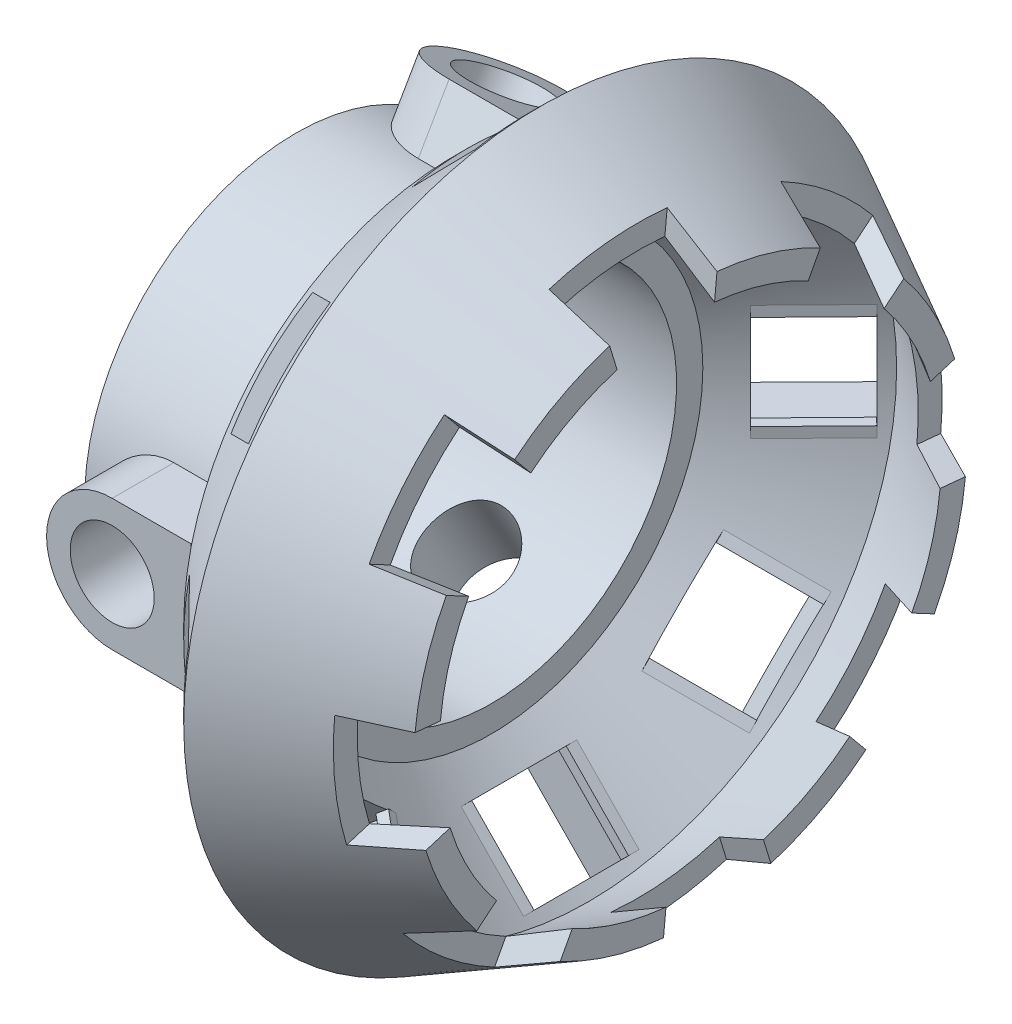
SolidWorks part; units mm, degrees
other "标注1"
sketch "草图8" plane through (-2.7147, -6.8585, 6.8585) normal (-0.2235, -0.0225, 0.9745) x (-0.1799, 0.9835, -0.0185)
ref_plane "前视基准面" through (0, 0, 0) normal (0, 0, 1) x (1, 0, 0)
ref_plane "上视基准面" through (0, 0, 0) normal (0, 1, 0) x (1, 0, 0)
ref_plane "右视基准面" through (0, 0, 0) normal (1, 0, 0) x (0, 0, -1)
sketch "草图1" plane through (0, 0, 0) normal (0, 0, 1) x (1, 0, 0)
  line L0 (0.7876, 3.525) -> (4.3576, 3.525)
  line L4 (4.7876, 4.025) -> (0.7876, 4.025)
  line L5 (0.7876, 4.025) -> (0.7876, 3.525)
  line L7 (7.7746, 6.7877) -> (11.1354, 5)
  line L8 (11.1354, 5) -> (11.1354, 4.5)
  line L9 (11.1354, 4.5) -> (8.6961, 5.8707)
  line L10 (4.3576, 3.525) -> (5.4612, 3.525) construction
  line L11 (7.6354, 5.8) -> (7.6354, 0) construction
  line L12 (0, 0) -> (8.3011, 0) construction
  line L13 (8.1304, 5.305) -> (7.6354, 5.8) construction
  line L14 (6.8503, 4.025) -> (8.6961, 5.8707)
  line L16 (11.1354, 4.5) -> (11.1354, -0.8919) construction
  line L17 (8.1304, 5.305) -> (11.1637, 2.2717) construction
  line L20 (4.7691, 3.525) -> (6.8503, 3.525)
  line L22 (4.3576, 3.525) -> (4.7691, 3.525)
  line L23 (6.1249, 5.138) -> (7.7746, 6.7877)
  line L24 (4.7876, 4.025) -> (7.3502, 4.025) construction
  line L25 (6.1249, 5.138) -> (6.1249, 4.025)
  line L26 (4.7876, 4.025) -> (6.1249, 4.025)
  line L27 (6.8503, 4.025) -> (6.8503, 3.525)
  dimension "D1" = 4.5
  dimension "D2" = 3.525
  dimension "D3" = 0.5
  dimension "D4" = 4
  dimension "D5" = 0.8
  dimension "D6" = 0.7
  dimension "D7" = 5.8
  dimension "D8" = 1.3
  dimension "D9" = 0.5
  dimension "D10" = 3.5
  dimension "D11" = 45
revolve "旋转1" add sketch "草图1" angle 360 about L12
sketch "草图2" plane through (0, 0, 0) normal (0, 1, 0) x (1, 0, 0)
  line L1 (3.0145, -5.257) -> (4.0717, -5.257) construction
  line L8 (6.1249, -5.138) -> (7.7746, -6.7877) construction
  line L9 (5.2766, -6.5082) -> (7.495, -4.2897)
  line L10 (5.2766, -6.5082) -> (6.4787, -7.7103)
  line L11 (6.4787, -7.7103) -> (8.6971, -5.4918)
  line L12 (7.495, -4.2897) -> (8.6971, -5.4918)
  line L13 (5.2766, -6.5082) -> (8.6971, -5.4918) construction
  line L14 (6.4787, -7.7103) -> (7.495, -4.2897) construction
  line L15 (0, 0) -> (-4.3641, 0) construction
  line L16 (6.9869, -6) -> (5.8776, -7.1092) construction
  line L17 (6.1249, -5.138) -> (7.7746, -6.7877) construction
  line L18 (6.1249, -5.138) -> (7.7746, -6.7877) construction
  line L19 (6.1249, -5.138) -> (7.7746, -6.7877) construction
  dimension "D1" = 45
  dimension "D2" = 1.7
  dimension "D3" = 6
extrude "切除-拉伸1" cut sketch "草图2" against normal mid plane 2.2
sketch "草图3" plane through (0, 0, 0) normal (0, 1, 0) x (1, 0, 0)
  line L0 (0, 0) -> (-2.7147, 0) construction
pattern_circular "阵列(圆周)1" count 8 over 360 about axis through (0, 0, 0) along (1, 0, 0) of "切除-拉伸1"
ref_plane "基准面2" through (1.5684, 0, -1.5316) normal (0.7155, 0, -0.6987) x (-0.6987, 0, -0.7155)
sketch "草图5" plane through (1.5684, 0, -1.5316) normal (0.7155, 0, -0.6987) x (-0.6987, 0, -0.7155)
  line L0 (-10.0078, 1.1) -> (-8.3076, 1.1)
  line L1 (-10.0078, 1.1) -> (-10.0078, 0.9)
  line L2 (-8.3076, 1.1) -> (-8.3076, 0.9)
  line L3 (-10.0078, 0.9) -> (-8.3076, 0.9)
  line L4 (-10.0078, -1.1) -> (-8.3076, -1.1)
  line L5 (-10.0078, -1.1) -> (-10.0078, -0.9)
  line L6 (-8.3076, -1.1) -> (-8.3076, -0.9)
  line L7 (-10.0078, -0.9) -> (-8.3076, -0.9)
  dimension "D1" = 0.2
  dimension "D2" = 0.2
extrude "凸台-拉伸1" add sketch "草图5" against normal blind 0.2
sketch "草图6" plane through (0, 0, 0) normal (0, 0, 1) x (1, 0, 0)
  line L0 (6.1249, 5.138) -> (6.1249, -5.138) construction
  line L1 (-2.939, 5.7136) -> (3.1249, 5.7136)
  line L2 (-2.939, 5.7136) -> (-2.939, -5.5135)
  line L3 (-2.939, -5.5135) -> (3.1249, -5.5135)
  line L4 (3.1249, 5.7136) -> (3.1249, -5.5135)
  line L5 (10.6354, 7.4147) -> (14.0576, 7.4147)
  line L6 (10.6354, 7.4147) -> (10.6354, -7.7149)
  line L7 (10.6354, -7.7149) -> (14.0576, -7.7149)
  line L8 (14.0576, 7.4147) -> (14.0576, -7.7149)
  line L9 (11.1354, -5) -> (11.1354, 5) construction
  dimension "D1" = 3
  dimension "D2" = 0.5
extrude "切除-拉伸2" cut sketch "草图6" against normal mid plane 20
ref_plane "基准面3" through (1.5684, -1.5316, 0) normal (-0.7155, 0.6987, 0) x (0, 0, 1)
sketch "草图7" plane through (1.5684, -1.5316, 0) normal (-0.7155, 0.6987, 0) x (0, 0, 1)
  line L0 (1.1, 10.0078) -> (1.1, 8.3076)
  line L1 (1.1, 10.0078) -> (0.9, 10.0078)
  line L2 (1.1, 8.3076) -> (0.9, 8.3076)
  line L3 (0.9, 10.0078) -> (0.9, 8.3076)
  line L4 (-1.1, 8.3076) -> (-1.1, 10.0078)
  line L5 (-1.1, 8.3076) -> (-0.9, 8.3076)
  line L6 (-1.1, 10.0078) -> (-0.9, 10.0078)
  line L7 (-0.9, 8.3076) -> (-0.9, 10.0078)
  dimension "D1" = 0.2
  dimension "D2" = 0.2
extrude "凸台-拉伸2" add sketch "草图7" along normal blind 0.2
pattern_circular "阵列(圆周)2" count 8 over 360 about axis through (0, 0, 0) along (1, 0, 0) of "凸台-拉伸2"
sketch "草图9" plane through (10.6354, 0, 0) normal (1, 0, 0) x (0, 0, -1)
  line L2 (0, 0) -> (-2.1978, 7.2108)
  line L3 (0, 0) -> (0.729, 7.503)
  line L4 (0, 0) -> (3.5447, 6.6529)
  line L5 (0, 0) -> (5.8208, 4.7899)
  line L6 (0, 0) -> (7.2108, 2.1978)
  line L7 (0, 0) -> (7.503, -0.729)
  line L8 (0, 0) -> (6.6529, -3.5447)
  line L9 (0, 0) -> (4.7899, -5.8208)
  line L10 (0, 0) -> (2.1978, -7.2108)
  line L11 (0, 0) -> (-0.729, -7.503)
  line L12 (0, 0) -> (-3.5447, -6.6529)
  line L13 (0, 0) -> (-5.8208, -4.7899)
  line L14 (0, 0) -> (-7.2108, -2.1978)
  line L15 (0, 0) -> (-7.503, 0.729)
  line L16 (0, 0) -> (-6.6529, 3.5447)
  line L17 (0, 0) -> (-4.7899, 5.8208)
  arc A2 (-2.1978, 7.2108) -> (0.729, 7.503) centre (0, 0) cw
  arc A4 (3.5447, 6.6529) -> (5.8208, 4.7899) centre (0, 0) cw
  arc A5 (7.2108, 2.1978) -> (7.503, -0.729) centre (0, 0) cw
  arc A6 (6.6529, -3.5447) -> (4.7899, -5.8208) centre (0, 0) cw
  arc A7 (2.1978, -7.2108) -> (-0.729, -7.503) centre (0, 0) cw
  arc A8 (-3.5447, -6.6529) -> (-5.8208, -4.7899) centre (0, 0) cw
  arc A9 (-7.2108, -2.1978) -> (-7.503, 0.729) centre (0, 0) cw
  arc A10 (-6.6529, 3.5447) -> (-4.7899, 5.8208) centre (0, 0) cw
  point P21 (0, 0)
  circle M4 centre (0, 0) radius 5.266
  circle M5 centre (0, 0) radius 4.781
  dimension "D1" = 22.5
  dimension "D2" = 8
extrude "切除-拉伸3" cut sketch "草图9" against normal blind 1 contours L8 L9 M5 | L9 L8 M5 M4 | A6 L8 L9 M4 | A7 L10 L11 M4 | L11 L10 M5 M4 | L10 L11 M5 | A8 L12 L13 M4 | L13 L12 M5 M4 | L12 L13 M5 | A9 L14 L15 M4 | L15 L14 M5 M4 | L14 L15 M5 | A10 L16 L17 M4 | L17 L16 M5 M4 | L16 L17 M5 | L2 L3 M5 | L3 L2 M5 M4 | A2 L2 L3 M4 | A4 L4 L5 M4 | L5 L4 M5 M4 | L4 L5 M5 | A5 L6 L7 M4 | L7 L6 M5 M4 | L6 L7 M5
ref_plane "基准面4" through (0, 0, 5) normal (0, 0, 1) x (1, 0, 0)
sketch "草图10" plane through (0, 0, 5) normal (0, 0, 1) x (1, 0, 0)
  line L0 (3.1249, 4.025) -> (3.1249, -4.025) construction
  line L1 (4.6249, -1.25) -> (6.1249, -1.25)
  line L2 (6.1249, 5.138) -> (6.1249, -5.138) construction
  line L3 (4.6249, 1.25) -> (6.1249, 1.25)
  line L4 (6.1249, -1.25) -> (6.1249, 1.25)
  circle A0 centre (4.6249, 0) radius 0.8
  arc A1 (4.6249, 1.25) -> (4.6249, -1.25) centre (4.6249, 0) ccw
  dimension "D1" = 1.6
  dimension "D2" = 2.5
  dimension "D3" = 1.5
extrude "凸台-拉伸3" add sketch "草图10" against normal blind 1.3
sketch "草图11" plane through (0, 0, 5) normal (0, 0, 1) x (1, 0, 0)
  circle A0 centre (4.6249, 0) radius 0.8
extrude "切除-拉伸4" cut sketch "草图11" against normal blind 1.8
pattern_circular "阵列(圆周)5" count 3 over 360 about axis through (0, 0, 0) along (1, 0, 0) of "切除-拉伸4", "凸台-拉伸3"
